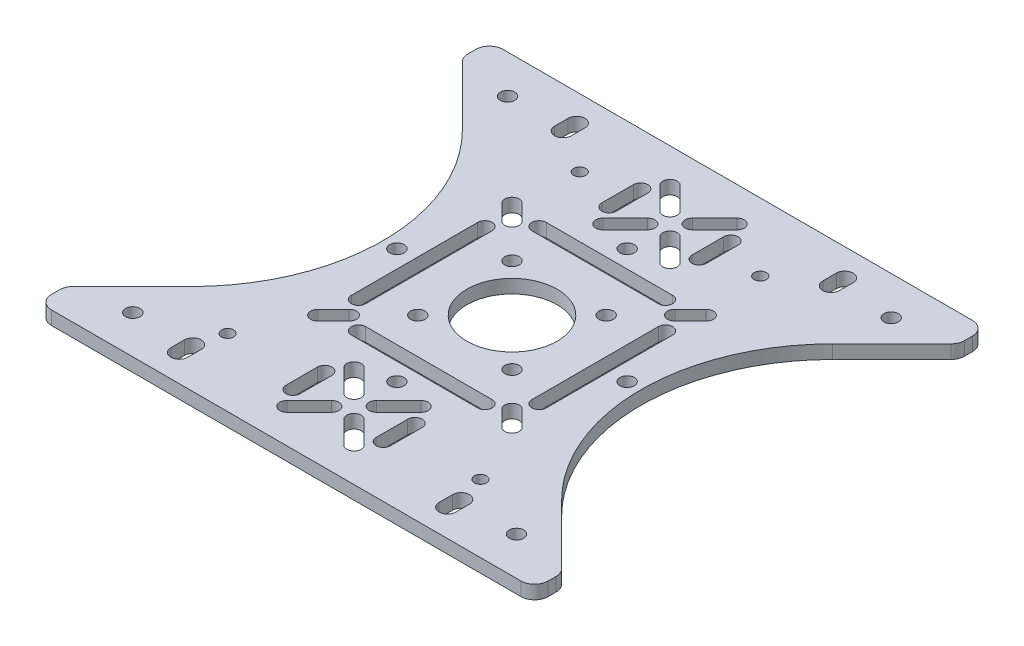
SolidWorks part; units mm, degrees
ref_plane "Front Plane" through (0, 0, 0) normal (0, 0, 1) x (1, 0, 0)
ref_plane "Top Plane" through (0, 0, 0) normal (0, 1, 0) x (1, 0, 0)
ref_plane "Right Plane" through (0, 0, 0) normal (1, 0, 0) x (0, 0, -1)
sketch "Sketch1" plane through (0, 0, 0) normal (0, 1, 0) x (1, 0, 0)
  line L0 (-55, 0) -> (55, 0) construction
  line L1 (-55, 50) -> (55, 50)
  line L2 (-55, 50) -> (-55, -50)
  line L3 (-55, -50) -> (55, -50)
  line L4 (55, 50) -> (55, -50)
  line L5 (-55, 50) -> (55, -50) construction
  line L6 (-55, -50) -> (55, 50) construction
  line L7 (-42.5, -41.5) -> (42.5, -41.5) construction
  line L8 (-42.5, -41.5) -> (-42.5, 41.5) construction
  line L9 (-42.5, 41.5) -> (42.5, 41.5) construction
  line L10 (42.5, -41.5) -> (42.5, 41.5) construction
  line L11 (-42.5, -41.5) -> (42.5, 41.5) construction
  line L12 (-42.5, 41.5) -> (42.5, -41.5) construction
  line L13 (0, 50) -> (0, -50) construction
  line L15 (-20, 35) -> (20, 35) construction
  line L16 (-20, 35) -> (-20, -35) construction
  line L17 (-20, -35) -> (20, -35) construction
  line L18 (20, 35) -> (20, -35) construction
  line L19 (-20, 35) -> (20, -35) construction
  line L20 (-20, -35) -> (20, 35) construction
  line L21 (-28, 35) -> (28, 35) construction
  line L22 (-28, 35) -> (-28, -35) construction
  line L23 (-28, -35) -> (28, -35) construction
  line L24 (28, 35) -> (28, -35) construction
  line L25 (-28, 35) -> (28, -35) construction
  line L26 (-28, -35) -> (28, 35) construction
  circle A0 centre (42.5, 41.5) radius 1.6
  circle A1 centre (20, 35) radius 1.35
  circle A2 centre (-20, 35) radius 1.35
  circle A3 centre (28, -35) radius 1.35
  circle A4 centre (-28, -35) radius 1.35
  circle A5 centre (-42.5, 41.5) radius 1.6
  circle A6 centre (42.5, -41.5) radius 1.6
  circle A7 centre (-42.5, -41.5) radius 1.6
  point P0 (0, 0)
  point P6 (0, 0)
  point P16 (0, 0)
  point P21 (0, 0)
  dimension "D5" = 3.2
  dimension "D10" = 2.7
  dimension "D11" = 2.7
  dimension "D1" = 110
  dimension "D2" = 100
  dimension "D3" = 85
  dimension "D4" = 83
  dimension "D6" = 70
  dimension "D7" = 40
  dimension "D8" = 70
  dimension "D9" = 56
extrude "Boss-Extrude1" add sketch "Sketch1" along normal blind 3
sketch "Sketch2" plane through (0, 3, 0) normal (0, 1, 0) x (1, 0, 0)
  line L0 (-14, 20) -> (14, 20) construction
  line L1 (-20, 20) -> (20, 20) construction
  line L2 (-20, 20) -> (-20, -20) construction
  line L3 (-20, -20) -> (20, -20) construction
  line L4 (20, 20) -> (20, -20) construction
  line L5 (-20, 20) -> (20, -20) construction
  line L6 (-20, -20) -> (20, 20) construction
  line L7 (-14, 21.6) -> (14, 21.6)
  line L8 (-14, 18.4) -> (14, 18.4)
  line L9 (0, 0) -> (29.6506, 0) construction
  line L10 (0, 0) -> (0, -14.4483) construction
  line L11 (-14, -20) -> (14, -20) construction
  line L12 (-14, -21.6) -> (14, -21.6)
  line L13 (-14, -18.4) -> (14, -18.4)
  line L14 (20, 14) -> (20, -14) construction
  line L15 (21.6, 14) -> (21.6, -14)
  line L16 (18.4, 14) -> (18.4, -14)
  line L17 (-20, 14) -> (-20, -14) construction
  line L18 (-21.6, 14) -> (-21.6, -14)
  line L19 (-18.4, 14) -> (-18.4, -14)
  line L20 (-21.5, 21.5) -> (-18.0312, 18.0312) construction
  line L21 (-21.5, 21.5) -> (21.5, 21.5) construction
  line L22 (-21.5, 21.5) -> (-21.5, -21.5) construction
  line L23 (-21.5, -21.5) -> (21.5, -21.5) construction
  line L24 (21.5, 21.5) -> (21.5, -21.5) construction
  line L25 (-21.5, 21.5) -> (21.5, -21.5) construction
  line L26 (-21.5, -21.5) -> (21.5, 21.5) construction
  line L27 (-20.3686, 22.6314) -> (-16.8999, 19.1626)
  line L28 (-22.6314, 20.3686) -> (-19.1626, 16.8999)
  line L29 (21.5, 21.5) -> (18.0312, 18.0312) construction
  line L30 (20.3686, 22.6314) -> (16.8999, 19.1626)
  line L31 (22.6314, 20.3686) -> (19.1626, 16.8999)
  line L32 (21.5, -21.5) -> (18.0312, -18.0312) construction
  line L33 (20.3686, -22.6314) -> (16.8999, -19.1626)
  line L34 (22.6314, -20.3686) -> (19.1626, -16.8999)
  line L35 (-21.5, -21.5) -> (-18.0312, -18.0312) construction
  line L36 (-20.3686, -22.6314) -> (-16.8999, -19.1626)
  line L37 (-22.6314, -20.3686) -> (-19.1626, -16.8999)
  circle A0 centre (0, 0) radius 10
  arc A1 (-14, 21.6) -> (-14, 18.4) centre (-14, 20) ccw
  arc A2 (14, 18.4) -> (14, 21.6) centre (14, 20) ccw
  arc A7 (-14, -21.6) -> (-14, -18.4) centre (-14, -20) cw
  arc A8 (14, -18.4) -> (14, -21.6) centre (14, -20) cw
  arc A9 (21.6, 14) -> (18.4, 14) centre (20, 14) ccw
  arc A10 (18.4, -14) -> (21.6, -14) centre (20, -14) ccw
  arc A11 (-21.6, 14) -> (-18.4, 14) centre (-20, 14) cw
  arc A12 (-18.4, -14) -> (-21.6, -14) centre (-20, -14) cw
  circle A32 centre (0, 0) radius 14.75 construction
  circle A33 centre (-10.4298, -10.4298) radius 1.6
  circle A34 centre (10.4298, -10.4298) radius 1.6
  circle A35 centre (-10.4298, 10.4298) radius 1.6
  circle A36 centre (10.4298, 10.4298) radius 1.6
  circle A41 centre (0, 0) radius 25.5 construction
  circle A42 centre (25.5, 0) radius 1.6
  circle A43 centre (0, -25.5) radius 1.6
  circle A44 centre (-25.5, 0) radius 1.6
  circle A45 centre (0, 25.5) radius 1.6
  arc A46 (-20.3686, 22.6314) -> (-22.6314, 20.3686) centre (-21.5, 21.5) ccw
  arc A47 (-19.1626, 16.8999) -> (-16.8999, 19.1626) centre (-18.0312, 18.0312) ccw
  arc A48 (20.3686, 22.6314) -> (22.6314, 20.3686) centre (21.5, 21.5) cw
  arc A49 (19.1626, 16.8999) -> (16.8999, 19.1626) centre (18.0312, 18.0312) cw
  arc A50 (20.3686, -22.6314) -> (22.6314, -20.3686) centre (21.5, -21.5) ccw
  arc A51 (19.1626, -16.8999) -> (16.8999, -19.1626) centre (18.0312, -18.0312) ccw
  arc A52 (-20.3686, -22.6314) -> (-22.6314, -20.3686) centre (-21.5, -21.5) cw
  arc A53 (-19.1626, -16.8999) -> (-16.8999, -19.1626) centre (-18.0312, -18.0312) cw
  point P9 (0, 20)
  point P14 (-19.7656, 19.7656)
  point P24 (0, -20)
  point P31 (20, 0)
  point P37 (20, 0)
  point P40 (-20, 0)
  point P69 (0, 0)
  point P72 (19.7656, 19.7656)
  point P78 (19.7656, -19.7656)
  point P84 (-19.7656, -19.7656)
  dimension "D1" = 20
  dimension "D6" = 3.2
  dimension "D9" = 29.5
  dimension "D10" = 3.2
  dimension "D11" = 43
  dimension "D13" = 51
  dimension "D14" = 3.2
  dimension "D2" = 40
  dimension "D3" = 40
  dimension "D4" = 28
  dimension "D5" = 3.2
  dimension "D7" = 3.2
  dimension "D8" = 28
  dimension "D12" = 43
  dimension "D15" = 4
extrude "Cut-Extrude1" cut sketch "Sketch2" against normal through all
sketch "Sketch3" plane through (0, 3, 0) normal (0, 1, 0) x (1, 0, 0)
  line L0 (0, 0) -> (20.272, 0) construction
  line L1 (0, 0) -> (0, 7.6403) construction
  line L2 (2.4749, 32.5251) -> (7.4246, 27.5754) construction
  line L3 (-10, 45) -> (10, 45) construction
  line L12 (-10, 45) -> (-10, 25) construction
  line L13 (-10, 25) -> (10, 25) construction
  line L14 (10, 45) -> (10, 25) construction
  line L15 (-10, 45) -> (10, 25) construction
  line L16 (-10, 25) -> (10, 45) construction
  line L17 (3.6062, 33.6565) -> (8.556, 28.7067)
  line L18 (1.3435, 31.3938) -> (6.2933, 26.444)
  line L19 (-2.4749, 32.5251) -> (-7.4246, 27.5754) construction
  line L20 (-1.3435, 31.3938) -> (-6.2933, 26.444)
  line L21 (-3.6062, 33.6565) -> (-8.556, 28.7067)
  line L22 (-2.4749, 37.4749) -> (-7.4246, 42.4246) construction
  line L23 (-3.6062, 36.3435) -> (-8.556, 41.2933)
  line L24 (-1.3435, 38.6062) -> (-6.2933, 43.556)
  line L25 (2.4749, 37.4749) -> (7.4246, 42.4246) construction
  line L26 (1.3435, 38.6062) -> (6.2933, 43.556)
  line L27 (3.6062, 36.3435) -> (8.556, 41.2933)
  line L28 (10, 38.5) -> (10, 31.5) construction
  line L29 (11.6, 38.5) -> (11.6, 31.5)
  line L30 (8.4, 38.5) -> (8.4, 31.5)
  line L31 (-10, 38.5) -> (-10, 31.5) construction
  line L32 (-11.6, 38.5) -> (-11.6, 31.5)
  line L33 (-8.4, 38.5) -> (-8.4, 31.5)
  line L34 (2.4749, -32.5251) -> (7.4246, -27.5754) construction
  line L35 (3.6062, -33.6565) -> (8.556, -28.7067)
  line L36 (1.3435, -31.3938) -> (6.2933, -26.444)
  line L37 (10, -38.5) -> (10, -31.5) construction
  line L38 (11.6, -38.5) -> (11.6, -31.5)
  line L39 (8.4, -38.5) -> (8.4, -31.5)
  line L40 (2.4749, -37.4749) -> (7.4246, -42.4246) construction
  line L41 (1.3435, -38.6062) -> (6.2933, -43.556)
  line L42 (3.6062, -36.3435) -> (8.556, -41.2933)
  line L43 (-2.4749, -32.5251) -> (-7.4246, -27.5754) construction
  line L44 (-1.3435, -31.3938) -> (-6.2933, -26.444)
  line L45 (-3.6062, -33.6565) -> (-8.556, -28.7067)
  line L46 (-10, -38.5) -> (-10, -31.5) construction
  line L47 (-11.6, -38.5) -> (-11.6, -31.5)
  line L48 (-8.4, -38.5) -> (-8.4, -31.5)
  line L49 (-2.4749, -37.4749) -> (-7.4246, -42.4246) construction
  line L50 (-3.6062, -36.3435) -> (-8.556, -41.2933)
  line L51 (-1.3435, -38.6062) -> (-6.2933, -43.556)
  line L52 (-56, 45) -> (-41, 30)
  line L58 (-55, 50) -> (-55, -50) construction
  line L59 (-41, 30) -> (-41, -30) construction
  line L60 (-41, -30) -> (-56, -45)
  line L61 (56, 45) -> (41, 30)
  line L62 (41, -30) -> (56, -45)
  line L63 (-56, 45) -> (-56, -45)
  line L65 (56, 45) -> (56, -45)
  line L66 (55, -50) -> (55, 50) construction
  arc A0 (3.6062, 33.6565) -> (1.3435, 31.3938) centre (2.4749, 32.5251) ccw
  arc A1 (6.2933, 26.444) -> (8.556, 28.7067) centre (7.4246, 27.5754) ccw
  circle A2 centre (0, 35) radius 7 construction
  arc A3 (-1.3435, 31.3938) -> (-3.6062, 33.6565) centre (-2.4749, 32.5251) ccw
  arc A4 (-8.556, 28.7067) -> (-6.2933, 26.444) centre (-7.4246, 27.5754) ccw
  arc A5 (-3.6062, 36.3435) -> (-1.3435, 38.6062) centre (-2.4749, 37.4749) ccw
  arc A6 (-6.2933, 43.556) -> (-8.556, 41.2933) centre (-7.4246, 42.4246) ccw
  arc A7 (1.3435, 38.6062) -> (3.6062, 36.3435) centre (2.4749, 37.4749) ccw
  arc A8 (8.556, 41.2933) -> (6.2933, 43.556) centre (7.4246, 42.4246) ccw
  arc A9 (11.6, 38.5) -> (8.4, 38.5) centre (10, 38.5) ccw
  arc A10 (8.4, 31.5) -> (11.6, 31.5) centre (10, 31.5) ccw
  arc A11 (-11.6, 38.5) -> (-8.4, 38.5) centre (-10, 38.5) cw
  arc A12 (-8.4, 31.5) -> (-11.6, 31.5) centre (-10, 31.5) cw
  arc A13 (3.6062, -33.6565) -> (1.3435, -31.3938) centre (2.4749, -32.5251) cw
  arc A14 (6.2933, -26.444) -> (8.556, -28.7067) centre (7.4246, -27.5754) cw
  arc A15 (11.6, -38.5) -> (8.4, -38.5) centre (10, -38.5) cw
  arc A16 (8.4, -31.5) -> (11.6, -31.5) centre (10, -31.5) cw
  arc A17 (1.3435, -38.6062) -> (3.6062, -36.3435) centre (2.4749, -37.4749) cw
  arc A18 (8.556, -41.2933) -> (6.2933, -43.556) centre (7.4246, -42.4246) cw
  arc A19 (-1.3435, -31.3938) -> (-3.6062, -33.6565) centre (-2.4749, -32.5251) cw
  arc A20 (-8.556, -28.7067) -> (-6.2933, -26.444) centre (-7.4246, -27.5754) cw
  arc A21 (-11.6, -38.5) -> (-8.4, -38.5) centre (-10, -38.5) ccw
  arc A22 (-8.4, -31.5) -> (-11.6, -31.5) centre (-10, -31.5) ccw
  arc A23 (-3.6062, -36.3435) -> (-1.3435, -38.6062) centre (-2.4749, -37.4749) cw
  arc A24 (-6.2933, -43.556) -> (-8.556, -41.2933) centre (-7.4246, -42.4246) cw
  arc A25 (-41, -30) -> (-41, 30) centre (-71, 0) ccw
  arc A26 (41, -30) -> (41, 30) centre (71, 0) cw
  point P1 (0, 35)
  point P13 (4.9497, 30.0503)
  point P20 (10, 35)
  point P25 (-4.9497, 30.0503)
  point P32 (-4.9497, 39.9497)
  point P39 (4.9497, 39.9497)
  point P44 (0, 35)
  point P51 (-10, 35)
  point P58 (4.9497, -30.0503)
  point P65 (10, -35)
  point P72 (4.9497, -39.9497)
  point P79 (-4.9497, -30.0503)
  point P86 (-10, -35)
  point P93 (-4.9497, -39.9497)
  point P101 (-41, 0)
  dimension "D6" = 14
  dimension "D14" = 1
  dimension "D1" = 20
  dimension "D2" = 20
  dimension "D3" = 35
  dimension "D4" = 3.2
  dimension "D5" = 7
  dimension "D8" = 3.2
  dimension "D9" = 7
  dimension "D10" = 45
  dimension "D11" = 45
  dimension "D12" = 90
  dimension "D13" = 60
  dimension "D7" = 4
extrude "Cut-Extrude2" cut sketch "Sketch3" against normal through all
fillet "Fillet2" radius 3 8 edges at (-55, 1.5, 50) (-55, 1.5, 44) (55, 1.5, 44) (55, 1.5, 50) (55, 1.5, -50) (55, 1.5, -44) (-55, 1.5, -50) (-55, 1.5, -44)
sketch "草图1" plane through (0, 3, 0) normal (0, 1, 0) x (1, 0, 0)
  line L0 (0, 0) -> (51.5643, 0) construction
  line L1 (0, -15.9512) -> (0, 15.9512) construction
  line L2 (-29.7, -41) -> (-29.7, -44) construction
  line L3 (-29.7, -42.5) -> (29.7, -42.5) construction
  line L4 (-29.7, -42.5) -> (-29.7, 42.5) construction
  line L5 (-29.7, 42.5) -> (29.7, 42.5) construction
  line L6 (29.7, -42.5) -> (29.7, 42.5) construction
  line L7 (-29.7, -42.5) -> (29.7, 42.5) construction
  line L8 (-29.7, 42.5) -> (29.7, -42.5) construction
  line L9 (-27.85, -41) -> (-27.85, -44)
  line L10 (-31.55, -41) -> (-31.55, -44)
  line L11 (29.7, -41) -> (29.7, -44) construction
  line L12 (27.85, -41) -> (27.85, -44)
  line L13 (31.55, -41) -> (31.55, -44)
  line L14 (29.7, 41) -> (29.7, 44) construction
  line L15 (27.85, 41) -> (27.85, 44)
  line L16 (31.55, 41) -> (31.55, 44)
  line L17 (-29.7, 41) -> (-29.7, 44) construction
  line L18 (-27.85, 41) -> (-27.85, 44)
  line L19 (-31.55, 41) -> (-31.55, 44)
  arc A0 (-27.85, -41) -> (-31.55, -41) centre (-29.7, -41) ccw
  arc A1 (-31.55, -44) -> (-27.85, -44) centre (-29.7, -44) ccw
  arc A2 (27.85, -41) -> (31.55, -41) centre (29.7, -41) cw
  arc A3 (31.55, -44) -> (27.85, -44) centre (29.7, -44) cw
  arc A4 (27.85, 41) -> (31.55, 41) centre (29.7, 41) ccw
  arc A5 (31.55, 44) -> (27.85, 44) centre (29.7, 44) ccw
  arc A6 (-27.85, 41) -> (-31.55, 41) centre (-29.7, 41) cw
  arc A7 (-31.55, 44) -> (-27.85, 44) centre (-29.7, 44) cw
  point P4 (0, 0)
  point P13 (-29.7, -42.5)
  point P21 (29.7, -42.5)
  point P28 (29.7, 42.5)
  point P35 (-29.7, 42.5)
  dimension "D1" = 59.4
  dimension "D2" = 85
  dimension "D3" = 3.7
  dimension "D4" = 3
extrude "切除-拉伸1" cut sketch "草图1" against normal through all
